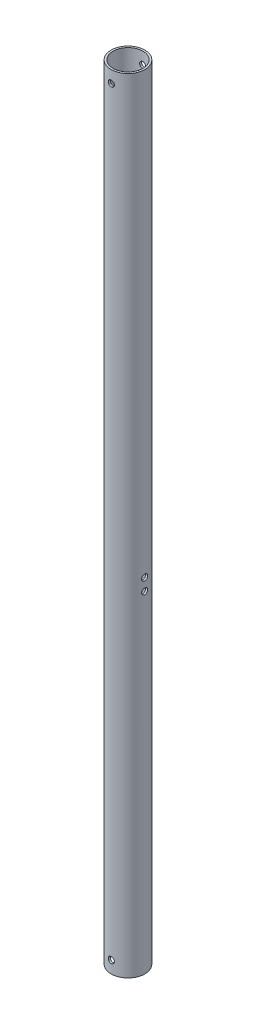
SolidWorks part; units mm, degrees
material "1060 Alloy"
ref_plane "Front Plane" through (0, 0, 0) normal (0, 0, 1) x (1, 0, 0)
ref_plane "Top Plane" through (0, 0, 0) normal (0, 1, 0) x (1, 0, 0)
ref_plane "Right Plane" through (0, 0, 0) normal (1, 0, 0) x (0, 0, -1)
sketch "Sketch1" plane through (0, 0, 0) normal (0, 1, 0) x (1, 0, 0)
  circle A0 centre (0, 0) radius 14
  circle A1 centre (0, 0) radius 12.4125
  dimension "D1" = 28
  dimension "D2" = 24.825
extrude "Boss-Extrude1" add sketch "Sketch1" along normal blind 650
sketch "Sketch2" plane through (0, 0, 0) normal (0, 0, 1) x (1, 0, 0)
  line L0 (12.4125, 650) -> (-12.4125, 650) construction
  circle A0 centre (0, 10) radius 2.5
  circle A1 centre (0, 640) radius 2.5
  dimension "D1" = 5
  dimension "D2" = 10
  dimension "D3" = 10
extrude "Cut-Extrude2" cut sketch "Sketch2" against normal through all both and the other way through all
ref_plane "Plane1" through (0, 500, 0) normal (0, 1, 0) x (1, 0, 0)
sketch "Sketch3" plane through (0, 500, 0) normal (0, 1, 0) x (1, 0, 0)
  circle A0 centre (0, 0) radius 17.5
  dimension "D1" = 35
ref_plane "Plane2" through (0, 100, 0) normal (0, 1, 0) x (1, 0, 0)
sketch "Sketch4" plane through (0, 0, 0) normal (0, 0, 1) x (1, 0, 0)
  line L0 (0, 650) -> (0, 0) construction
  line L1 (14, 650) -> (-14, 650) construction
sketch "Sketch6" plane through (0, 0, 0) normal (1, 0, 0) x (0, 0, -1)
  line L0 (-14, 0) -> (14, 0) construction
  circle A0 centre (0, 285) radius 2.5
  circle A1 centre (0, 275) radius 2.5
  dimension "D1" = 5
  dimension "D2" = 10
  dimension "D3" = 275
extrude "Cut-Extrude4" cut sketch "Sketch6" against normal through all both and the other way through all
equation "\"keelOutDiameter\"= 1in"
equation "\"poleOutDiameter\"= 28mm"
equation "\"poleLength\"=650mm"
equation "\"D1@Sketch1\"=\"poleOutDiameter\""
equation "\"D2@Sketch1\"=\"poleOutDiameter\"-0.125in"
